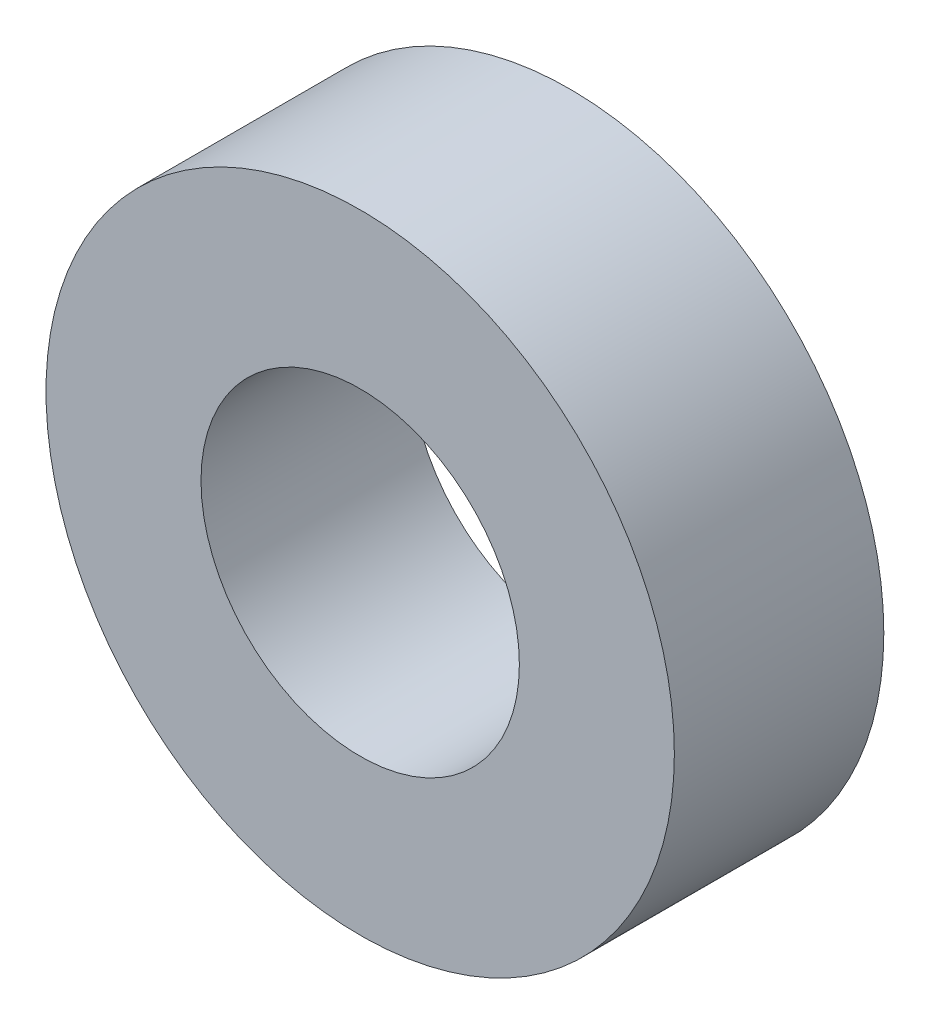
SolidWorks part; units mm, degrees
ref_plane "Front Plane" through (0, 0, 0) normal (0, 0, 1) x (1, 0, 0)
ref_plane "Top Plane" through (0, 0, 0) normal (0, 1, 0) x (1, 0, 0)
ref_plane "Right Plane" through (0, 0, 0) normal (1, 0, 0) x (0, 0, -1)
sketch "Sketch1" plane through (0, 0, 0) normal (0, 0, 1) x (1, 0, 0)
  circle A0 centre (0, 0) radius 9.525
  circle A1 centre (0, 0) radius 4.826
  dimension "OD" = 19.05
  dimension "ID" = 9.652
extrude "Extrude1" add sketch "Sketch1" along normal mid plane 6.35
sketch "Sketch2" plane through (0, 0, 0) normal (1, 0, 0) x (0, 0, -1)
  line L0 (-3.175, -4.826) -> (3.175, -4.826) construction
  line L3 (3.175, 4.826) -> (-3.175, 4.826) construction
  line L5 (-3.175, -4.826) -> (3.175, -4.826)
  line L6 (3.175, 4.826) -> (-3.175, 4.826)
sketch "Sketch4" plane through (0, 0, 3.175) normal (0, 0, 1) x (1, 0, 0)
  line L0 (0, 0) -> (-3.4125, 3.4125)
  line L1 (0, -2.1828) -> (0, 2.1828) construction
  circle A0 centre (0, 0) radius 4.826 construction
  dimension "D1" = 45
